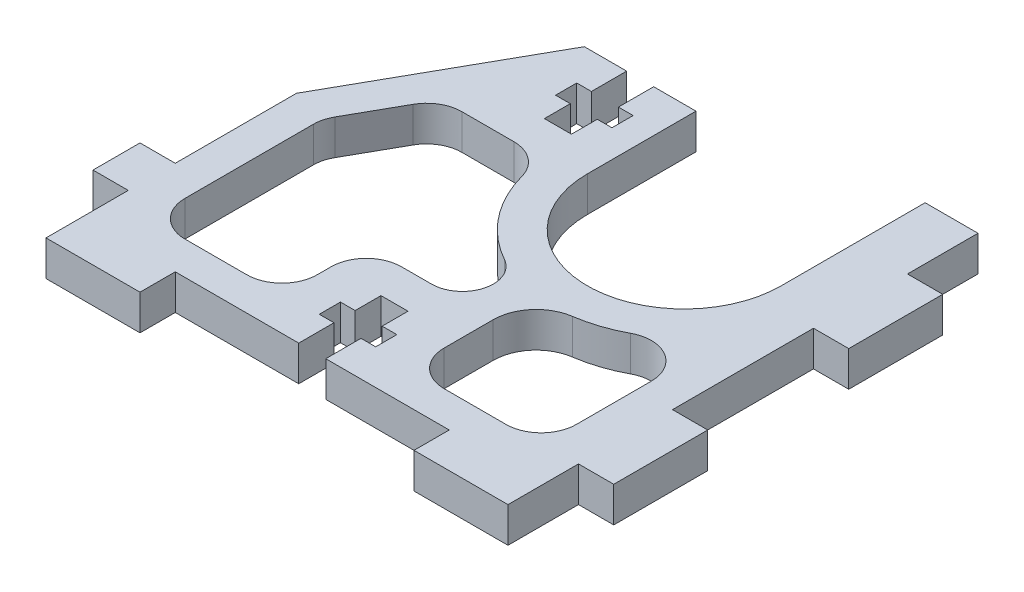
SolidWorks part; units mm, degrees
ref_plane "Front Plane" through (0, 0, 0) normal (0, 0, 1) x (1, 0, 0)
ref_plane "Top Plane" through (0, 0, 0) normal (0, 1, 0) x (1, 0, 0)
ref_plane "Right Plane" through (0, 0, 0) normal (1, 0, 0) x (0, 0, -1)
sketch "Sketch1" plane through (0, 0, 0) normal (0, 1, 0) x (1, 0, 0)
  line L1 (15.25, 17) -> (-15.25, 17)
  line L2 (15.25, 17) -> (15.25, -17)
  line L3 (15.25, -17) -> (-15.25, -17)
  line L4 (-15.25, 17) -> (-15.25, -17)
  line L5 (15.25, 17) -> (-15.25, -17) construction
  line L6 (15.25, -17) -> (-15.25, 17) construction
  point P0 (0, 0)
  dimension "D1" = 30.5
  dimension "D2" = 34
extrude "Boss-Extrude1" add sketch "Sketch1" along normal mid plane 3
sketch "Sketch2" plane through (0, 1.5, 0) normal (0, 1, 0) x (1, 0, 0)
  line L1 (-15.25, 17) -> (-24.07, 1.309)
  line L2 (-55.3828, -17) -> (-15.25, -17)
  line L3 (-15.25, -17) -> (15.25, -17) construction
  line L4 (-15.25, 17) -> (-15.25, -17)
  line L6 (-55.3828, -17) -> (-55.3828, -27.8535) construction
  spline S0 degree 3 poles (-24.07, 1.309) (-25.6121, -1.4345) (-30.226, -1.523) (-46.6978, -11.0884) (-55.3828, -10.3072) (-55.3828, -17) knots 0 0 0 0 0.22113 0.6036 1 1 1 1
  dimension "D2" = 8.82
  dimension "D1" = 18
extrude "Boss-Extrude2" add sketch "Sketch2" against normal up to vertex (3 mm away)
sketch "Sketch3" plane through (0, 1.5, 0) normal (0, 1, 0) x (1, 0, 0)
  line L0 (15.25, -17) -> (15.25, 17) construction
  line L1 (15.25, 14) -> (18.25, 14)
  line L2 (15.25, 14) -> (15.25, 6)
  line L3 (15.25, 6) -> (18.25, 6)
  line L4 (18.25, 14) -> (18.25, 6)
  line L5 (16.75, -6) -> (16.75, 6) construction
  line L6 (15.25, -6) -> (18.25, -6)
  line L7 (15.25, -6) -> (15.25, -14)
  line L8 (15.25, -14) -> (18.25, -14)
  line L9 (18.25, -6) -> (18.25, -14)
  line L10 (0, 0) -> (16.75, 0) construction
  line L11 (-55.3828, -17) -> (15.25, -17) construction
  line L12 (-15.25, 17) -> (-7.25, 17)
  line L13 (-15.25, 17) -> (-15.25, 20)
  line L14 (-15.25, 20) -> (-7.25, 20)
  line L15 (-7.25, 17) -> (-7.25, 20)
  line L16 (15.25, 17) -> (7.25, 17)
  line L17 (15.25, 17) -> (15.25, 20)
  line L18 (15.25, 20) -> (7.25, 20)
  line L19 (7.25, 17) -> (7.25, 20)
  line L20 (-55.3828, -17) -> (-47.3828, -17)
  line L21 (-55.3828, -17) -> (-55.3828, -20)
  line L22 (-55.3828, -20) -> (-47.3828, -20)
  line L23 (-47.3828, -17) -> (-47.3828, -20)
  line L24 (15.25, -17) -> (7.25, -17)
  line L25 (15.25, -17) -> (15.25, -20)
  line L26 (15.25, -20) -> (7.25, -20)
  line L27 (7.25, -17) -> (7.25, -20)
  line L28 (-24.0664, -17) -> (-16.0664, -17)
  line L29 (-24.0664, -17) -> (-24.0664, -20)
  line L30 (-24.0664, -20) -> (-16.0664, -20)
  line L31 (-16.0664, -17) -> (-16.0664, -20)
  line L32 (-47.3828, -18.5) -> (-24.0664, -18.5) construction
  line L33 (-16.0664, -18.5) -> (7.25, -18.5) construction
  dimension "D1" = 3
  dimension "D2" = 8
  dimension "D3" = 12
extrude "Boss-Extrude3" add sketch "Sketch3" against normal up to vertex (3 mm away)
sketch "Sketch4" plane through (0, 1.5, 0) normal (0, 1, 0) x (1, 0, 0)
  line L0 (7.25, 17) -> (-7.25, 17) construction
  line L1 (-1.15, 17) -> (1.15, 17)
  line L2 (-1.15, 17) -> (-1.15, 14)
  line L3 (-1.15, 10) -> (1.15, 10)
  line L4 (1.15, 17) -> (1.15, 14)
  line L5 (0, 0) -> (0, 10) construction
  line L6 (1.15, 12.2) -> (2.4, 12.2)
  line L7 (-2.4, 14) -> (-1.15, 14)
  line L8 (-2.4, 14) -> (-2.4, 12.2)
  line L9 (-2.4, 12.2) -> (-1.15, 12.2)
  line L10 (2.4, 14) -> (2.4, 12.2)
  line L11 (-1.15, 12.2) -> (-1.15, 10)
  line L12 (1.15, 12.2) -> (1.15, 10)
  line L13 (1.15, 14) -> (2.4, 14)
  line L14 (-2.0082, -12.2) -> (-3.2582, -12.2)
  line L15 (-5.5582, -12.2) -> (-6.8082, -12.2)
  line L16 (-3.2582, -17) -> (-5.5582, -17)
  line L17 (-5.5582, -12.2) -> (-5.5582, -10)
  line L18 (-3.2582, -12.2) -> (-3.2582, -10)
  line L19 (-2.0082, -14) -> (-2.0082, -12.2)
  line L20 (-3.2582, -10) -> (-5.5582, -10)
  line L21 (-6.8082, -14) -> (-6.8082, -12.2)
  line L22 (-5.5582, -14) -> (-6.8082, -14)
  line L23 (-3.2582, -17) -> (-3.2582, -14)
  line L24 (-5.5582, -17) -> (-5.5582, -14)
  line L25 (-2.0082, -14) -> (-3.2582, -14)
  line L26 (-33.3246, -12.2) -> (-34.5746, -12.2)
  line L27 (-36.8746, -12.2) -> (-38.1246, -12.2)
  line L28 (-34.5746, -17) -> (-36.8746, -17)
  line L29 (-36.8746, -12.2) -> (-36.8746, -10)
  line L30 (-34.5746, -12.2) -> (-34.5746, -10)
  line L31 (-33.3246, -14) -> (-33.3246, -12.2)
  line L32 (-34.5746, -10) -> (-36.8746, -10)
  line L33 (-38.1246, -14) -> (-38.1246, -12.2)
  line L34 (-36.8746, -14) -> (-38.1246, -14)
  line L35 (-34.5746, -17) -> (-34.5746, -14)
  line L36 (-36.8746, -17) -> (-36.8746, -14)
  line L37 (-33.3246, -14) -> (-34.5746, -14)
  line L38 (-4.4082, -17) -> (-4.4082, -10) construction
  line L39 (-16.0664, -17) -> (7.25, -17) construction
  line L40 (-35.7246, -17) -> (-35.7246, -10) construction
  line L41 (-47.3828, -17) -> (-24.0664, -17) construction
  point P49 (-35.7246, -17)
  line M13 (-47.3828, -17) -> (-24.0664, -17)
  line M17 (-16.0664, -17) -> (7.25, -17)
  dimension "D1" = 2.3
  dimension "D2" = 7
  dimension "D3" = 4.8
  dimension "D4" = 3
  dimension "D5" = 1.8
  dimension "D6" = 2.3
  dimension "D7" = 7
  dimension "D8" = 4.8
  dimension "D9" = 1.8
  dimension "D10" = 2.3
  dimension "D11" = 7
  dimension "D12" = 4.8
  dimension "D13" = 1.8
  dimension "D14" = 3
  dimension "D15" = 3
extrude "Cut-Extrude1" cut sketch "Sketch4" against normal through all contours L25 L19 L14 L18 L20 L17 L15 L21 L22 L24 L23 M17 | L37 L31 L26 L30 L32 L29 L27 L33 L34 L36 L35 M13
sketch "Sketch5" plane through (0, 1.5, 0) normal (0, 1, 0) x (1, 0, 0)
  line L0 (10.75, 20) -> (10.75, 7.75)
  line L1 (15.25, 20) -> (7.25, 20) construction
  line L3 (-5.75, 20) -> (-5.75, 7.75)
  line L10 (-5.75, 20) -> (10.75, 20)
  line L11 (15.25, 14) -> (15.25, 20) construction
  arc A0 (-5.75, 7.75) -> (10.75, 7.75) centre (2.5, 7.75) ccw
  dimension "D1" = 20.5
  dimension "D2" = 4.5
  dimension "D3" = 16.5
extrude "Cut-Extrude2" cut sketch "Sketch5" against normal through all
sketch "Sketch6" plane through (0, 1.5, 0) normal (0, 1, 0) x (1, 0, 0)
  line L1 (-7.25, 17) -> (-15.25, 17)
  line L2 (-7.25, 17) -> (-7.25, 20)
  line L3 (-7.25, 20) -> (-15.25, 20)
  line L4 (-15.25, 17) -> (-15.25, 20)
extrude "Cut-Extrude3" cut sketch "Sketch6" against normal through all
sketch "Sketch7" plane through (0, 1.5, 0) normal (0, 1, 0) x (1, 0, 0)
  line L0 (-5.75, 17) -> (-15.25, 17) construction
  line L1 (-11.65, 17) -> (-9.35, 17)
  line L2 (-11.65, 17) -> (-11.65, 14)
  line L3 (-11.65, 10) -> (-9.35, 10)
  line L4 (-9.35, 17) -> (-9.35, 14)
  line L5 (-11.65, 12.2) -> (-11.65, 10)
  line L6 (-12.9, 14) -> (-11.65, 14)
  line L7 (-12.9, 14) -> (-12.9, 12.2)
  line L8 (-12.9, 12.2) -> (-11.65, 12.2)
  line L9 (-8.1, 14) -> (-8.1, 12.2)
  line L10 (-9.35, 12.2) -> (-8.1, 12.2)
  line L11 (-9.35, 12.2) -> (-9.35, 10)
  line L12 (-9.35, 14) -> (-8.1, 14)
  line L13 (-10.5, 10) -> (-10.5, 17) construction
  point P16 (-10.5, 17)
  dimension "D1" = 2.3
  dimension "D2" = 1.8
  dimension "D3" = 4.8
  dimension "D4" = 3
  dimension "D5" = 7
extrude "Cut-Extrude4" cut sketch "Sketch7" against normal through all
sketch "Sketch8" plane through (0, 1.5, 0) normal (0, 1, 0) x (1, 0, 0)
  line L0 (-24.0664, -17) -> (-24.0664, 1.3154)
  line L2 (-15.25, 17) -> (-24.07, 1.309) construction
  line L63 (-12.9, 14) -> (-11.65, 14)
  line L64 (-11.65, 14) -> (-11.65, 17)
  line L65 (-11.65, 17) -> (-15.25, 17)
  line L66 (-15.25, 17) -> (-24.07, 1.309)
  line L67 (-55.3828, -17) -> (-55.3828, -20)
  line L68 (-55.3828, -20) -> (-47.3828, -20)
  line L69 (-47.3828, -20) -> (-47.3828, -17)
  line L70 (-47.3828, -17) -> (-36.8746, -17)
  line L71 (-36.8746, -17) -> (-36.8746, -14)
  line L72 (-36.8746, -14) -> (-38.1246, -14)
  line L73 (-38.1246, -14) -> (-38.1246, -12.2)
  line L74 (-38.1246, -12.2) -> (-36.8746, -12.2)
  line L75 (-36.8746, -12.2) -> (-36.8746, -10)
  line L76 (-36.8746, -10) -> (-34.5746, -10)
  line L77 (-34.5746, -10) -> (-34.5746, -12.2)
  line L78 (-34.5746, -12.2) -> (-33.3246, -12.2)
  line L79 (-33.3246, -12.2) -> (-33.3246, -14)
  line L80 (-33.3246, -14) -> (-34.5746, -14)
  line L81 (-34.5746, -14) -> (-34.5746, -17)
  line L82 (-34.5746, -17) -> (-24.0664, -17)
  line L83 (-24.0664, -17) -> (-24.0664, -20)
  line L84 (-24.0664, -20) -> (-16.0664, -20)
  line L85 (-16.0664, -20) -> (-16.0664, -17)
  line L86 (-16.0664, -17) -> (-5.5582, -17)
  line L87 (-5.5582, -17) -> (-5.5582, -14)
  line L88 (-5.5582, -14) -> (-6.8082, -14)
  line L89 (-6.8082, -14) -> (-6.8082, -12.2)
  line L90 (-6.8082, -12.2) -> (-5.5582, -12.2)
  line L91 (-5.5582, -12.2) -> (-5.5582, -10)
  line L92 (-5.5582, -10) -> (-3.2582, -10)
  line L93 (-3.2582, -10) -> (-3.2582, -12.2)
  line L94 (-3.2582, -12.2) -> (-2.0082, -12.2)
  line L95 (-2.0082, -12.2) -> (-2.0082, -14)
  line L96 (-2.0082, -14) -> (-3.2582, -14)
  line L97 (-3.2582, -14) -> (-3.2582, -17)
  line L98 (-3.2582, -17) -> (7.25, -17)
  line L99 (7.25, -17) -> (7.25, -20)
  line L100 (7.25, -20) -> (15.25, -20)
  line L101 (15.25, -20) -> (15.25, -14)
  line L102 (15.25, -14) -> (18.25, -14)
  line L103 (18.25, -14) -> (18.25, -6)
  line L104 (18.25, -6) -> (15.25, -6)
  line L105 (15.25, -6) -> (15.25, 6)
  line L106 (15.25, 6) -> (18.25, 6)
  line L107 (18.25, 6) -> (18.25, 14)
  line L108 (18.25, 14) -> (15.25, 14)
  line L109 (15.25, 14) -> (15.25, 20)
  line L110 (15.25, 20) -> (10.75, 20)
  line L111 (10.75, 20) -> (10.75, 7.75)
  line L112 (-5.75, 7.75) -> (-5.75, 17)
  line L113 (-5.75, 17) -> (-9.35, 17)
  line L114 (-9.35, 17) -> (-9.35, 14)
  line L115 (-9.35, 14) -> (-8.1, 14)
  line L116 (-8.1, 14) -> (-8.1, 12.2)
  line L117 (-8.1, 12.2) -> (-9.35, 12.2)
  line L118 (-9.35, 12.2) -> (-9.35, 10)
  line L119 (-9.35, 10) -> (-11.65, 10)
  line L120 (-11.65, 10) -> (-11.65, 12.2)
  line L121 (-11.65, 12.2) -> (-12.9, 12.2)
  line L122 (-12.9, 12.2) -> (-12.9, 14)
  line L126 (-24.0664, 1.3154) -> (-24.07, 1.309)
  line L127 (-55.3828, -17) -> (-55.3828, -20)
  line L128 (-55.3828, -20) -> (-47.3828, -20)
  line L129 (-47.3828, -20) -> (-47.3828, -17)
  line L130 (-47.3828, -17) -> (-36.8746, -17)
  line L131 (-36.8746, -17) -> (-36.8746, -14)
  line L132 (-36.8746, -14) -> (-38.1246, -14)
  line L133 (-38.1246, -14) -> (-38.1246, -12.2)
  line L134 (-38.1246, -12.2) -> (-36.8746, -12.2)
  line L135 (-36.8746, -12.2) -> (-36.8746, -10)
  line L136 (-36.8746, -10) -> (-34.5746, -10)
  line L137 (-34.5746, -10) -> (-34.5746, -12.2)
  line L138 (-34.5746, -12.2) -> (-33.3246, -12.2)
  line L139 (-33.3246, -12.2) -> (-33.3246, -14)
  line L140 (-33.3246, -14) -> (-34.5746, -14)
  line L141 (-34.5746, -14) -> (-34.5746, -17)
  line L142 (-34.5746, -17) -> (-24.0664, -17)
  arc A1 (-5.75, 7.75) -> (10.75, 7.75) centre (2.5, 7.75) ccw
  spline S1 degree 3 poles (224.7586, 1985.7153) (-40.4807, -43.8615) (-2.9101, 14.3397) (-79.7572, -30.2865) (-72.6227, 48.3771) (718.9285, -1860.9983) knots -1.65834 -1.65834 -1.65834 -1.65834 0.22113 0.6036 3.007027 3.007027 3.007027 3.007027 only from (-24.07, 1.309) to (-55.3828, -17)
  spline S2 degree 3 poles (-24.07, 1.309) (-25.6121, -1.4345) (-30.226, -1.523) (-46.6978, -11.0884) (-55.3828, -10.3072) (-55.3828, -17) knots 0 0 0 0 0.22113 0.6036 1 1 1 1
  dimension "D1" = 0
extrude "Cut-Extrude6" cut sketch "Sketch8" against normal through all
sketch "Sketch9" plane through (0, 1.5, 0) normal (0, 1, 0) x (1, 0, 0)
  line L0 (-24.0664, 1.3154) -> (-24.0664, -20) construction
  line L1 (-24.0664, -9) -> (-27.0664, -9)
  line L2 (-24.0664, -9) -> (-24.0664, -13)
  line L3 (-24.0664, -13) -> (-27.0664, -13)
  line L4 (-27.0664, -9) -> (-27.0664, -13)
  line L5 (-24.0664, -9) -> (-27.0664, -9) construction
  line L6 (-24.0664, -13) -> (-27.0664, -13) construction
  line L7 (-27.0664, -13) -> (-27.0664, -9) construction
extrude "Boss-Extrude4" add sketch "Sketch9" against normal up to vertex (3 mm away)
sketch "Sketch10" plane through (0, 1.5, 0) normal (0, 1, 0) x (1, 0, 0)
  line L0 (-21.0664, 0.5301) -> (-21.0664, -14.173)
  line L1 (-21.0664, -14.173) -> (-9.8082, -14.173)
  line L2 (-9.8082, -14.173) -> (-9.8082, -7)
  line L3 (-9.8082, -7) -> (0.9918, -7)
  line L4 (0.9918, -7) -> (0.9918, -14.173)
  line L5 (0.9918, -14.173) -> (12.25, -14.173)
  line L6 (12.25, -14.173) -> (12.25, 2.1375)
  line L7 (-2.0082, -13.1) -> (0.9918, -13.1) construction
  line L8 (-2.0082, -14) -> (-2.0082, -12.2) construction
  line L9 (-8.725, 7) -> (-17.4296, 7)
  line L10 (-17.4296, 7) -> (-21.0664, 0.5301)
  line L11 (-15.25, 17) -> (-24.0664, 1.3154) construction
  line L12 (-4.4082, -10) -> (-4.4082, -7) construction
  line L13 (-3.2582, -10) -> (-5.5582, -10) construction
  line L14 (12.25, 2.1375) -> (15.25, 2.1375) construction
  line L15 (15.25, -6) -> (15.25, 6) construction
  line L16 (0.9918, -14.173) -> (1.9959, -17) construction
  line L17 (-3.2582, -17) -> (7.25, -17) construction
  line L18 (-9.8082, -14.173) -> (-10.8123, -17) construction
  line L19 (-16.0664, -17) -> (-5.5582, -17) construction
  line L20 (-21.0664, 0.5301) -> (-24.0664, 0.5301) construction
  line L21 (-17.4296, 7) -> (-20.0448, 8.47) construction
  line L22 (-10.5, 10) -> (-10.5, 7) construction
  line L23 (-11.65, 10) -> (-9.35, 10) construction
  line L25 (-24.0664, 1.3154) -> (-24.0664, -9) construction
  arc A3 (-8.75, 7.75) -> (13.75, 7.75) centre (2.5, 7.75) ccw
  arc A4 (-8.725, 7) -> (12.25, 2.1375) centre (2.5, 7.75) ccw
  dimension "D1" = 3
  dimension "D2" = 3
extrude "Cut-Extrude7" cut sketch "Sketch10" against normal through all
fillet "Fillet1" radius 3 9 edges at (-9.8082, 0, 7) (12.25, 0, -2.1375) (-21.0664, 0, -0.5301) (-17.4296, 0, -7) (-8.725, 0, -7) (12.25, 0, 14.173) (0.9918, 0, 14.173) (-9.8082, 0, 14.173) (-21.0664, 0, 14.173)
sketch "Sketch11" plane through (0, 1.5, 0) normal (0, 1, 0) x (1, 0, 0)
  line L0 (0.9918, -7) -> (0.9918, -11.173) construction
  line L1 (-6.8082, -7) -> (0.9918, -7) construction
  line L2 (-4.2563, -7) -> (0.9918, -7)
  arc A0 (4.1207, -3.3826) -> (0.9918, -7) centre (4.6473, -7) ccw
  arc A1 (-8.3535, 4.7895) -> (7.8289, -2.1578) centre (2.5, 7.75) ccw construction
  arc A2 (-4.2563, -7) -> (-2.977, -2.0768) centre (-4.2563, -4.3722) ccw
  arc A3 (-2.977, -2.0768) -> (4.1207, -3.3826) centre (2.5, 7.75) ccw
  dimension "D1" = 3
extrude "Boss-Extrude5" add sketch "Sketch11" against normal up to vertex (3 mm away)
